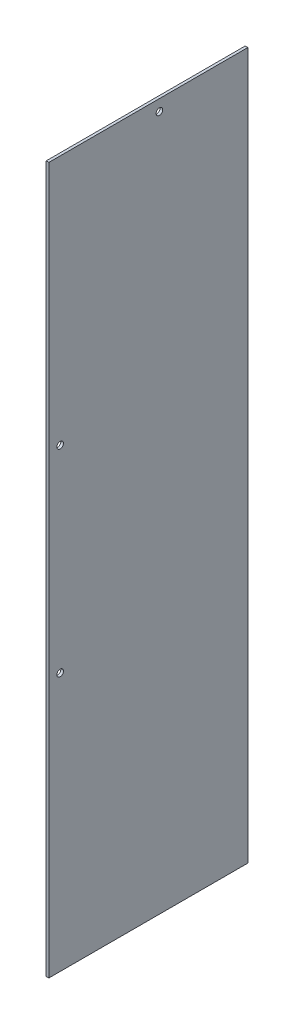
SolidWorks part; units mm, degrees
material "Acrylic (Medium-high impact)"
ref_plane "Front Plane" through (0, 0, 0) normal (0, 0, 1) x (1, 0, 0)
ref_plane "Top Plane" through (0, 0, 0) normal (0, 1, 0) x (1, 0, 0)
ref_plane "Right Plane" through (0, 0, 0) normal (1, 0, 0) x (0, 0, -1)
sketch "Sketch1" plane through (0, 0, 0) normal (1, 0, 0) x (0, 0, -1)
  line L1 (114.4905, -406.5905) -> (-114.4905, -406.5905)
  line L2 (114.4905, -406.5905) -> (114.4905, 406.5905)
  line L3 (114.4905, 406.5905) -> (-114.4905, 406.5905)
  line L4 (-114.4905, -406.5905) -> (-114.4905, 406.5905)
  line L5 (114.4905, -406.5905) -> (-114.4905, 406.5905) construction
  line L6 (114.4905, 406.5905) -> (-114.4905, -406.5905) construction
  point P0 (0, 0)
  dimension "D1" = 813.181
  dimension "D2" = 228.981
extrude "Boss-Extrude1" add sketch "Sketch1" along normal blind 3.0734
sketch "Sketch2" plane through (3.0734, 0, 0) normal (1, 0, 0) x (0, 0, -1)
  line L0 (-114.4905, 406.5905) -> (-114.4905, -406.5905) construction
  line L1 (114.4905, 406.5905) -> (-114.4905, 406.5905) construction
  circle A0 centre (12.7889, 393.6111) radius 3.81
  circle A1 centre (-101.5111, 118.165) radius 3.81
  circle A2 centre (-101.5111, -108.9194) radius 3.81
  dimension "D1" = 7.62
  dimension "D2" = 127.2794
  dimension "D3" = 12.9794
  dimension "D4" = 12.9794
  dimension "D5" = 288.4255
  dimension "D6" = 227.0845
extrude "Cut-Extrude1" cut sketch "Sketch2" against normal up to next
equation "\"Height\"= 32in"
equation "\"Width\"= 23in"
equation "\"Depth\"= 20in"
equation "\"Plexi\"= .121in"
equation "\"EBWidth\" = 9in"
equation "\"MagnetThickness\"= 0.125in"
equation "\"MagnetDiameter\"= 12mm"
equation "\"DoorPlexi\" = \"Plexi\""
equation "\"BasePlateThickness\" = 0.5in"
equation "\"BasePlateWidth\" = \"Width\"+\"EBWidth\"-2*\"Plexi\""
equation "\"BasePlateDepth\" = \"TopBarDepth\"+2*\"CornerCube\""
equation "\"Boxsize\" = .75in"
equation "\"BoxsizeHalf\" = \"Boxsize\"/2"
equation "\"Boxinner\" = .625in"
equation "\"CornerCube\" = 0.75in"
equation "\"FingerLength\" = 1.125in"
equation "\"FingerWidth\" = .625in"
equation "\"Cutwidth\"= .016in"
equation "\"Earsize\"= 1in + \"Cutwidth\" /2"
equation "\"Slotsize\" = 1in - \"CutWidth\" / 2"
equation "\"InnerWidth\" = \"Width\" - 2* \"Plexi\""
equation "\"InnerHeight\" = \"Height\" -2 * \"Plexi\""
equation "\"InnerDepth\" = \"Depth\" - 2*\"Plexi\""
equation "\"RearNumHoles\" = 4"
equation "\"RearHolesBorder\" = 2.25"
equation "\"RearHoleSpacing\" = (\"Width\" - 2*\"RearHolesBorder\") / (\"RearNumHoles\"-1)"
equation "\"RearBarLength\" = (\"InnerWidth\"-2*\"CornerCube\")"
equation "\"RearTopNumHoles\" = 4"
equation "\"RearTopHolesBorder\" = 3.1"
equation "\"RearTopHolesSpacing\" = (\"Width\" - 2*\"RearTopHolesBorder\") / (\"RearTopNumHoles\"-1)"
equation "\"SideTopNumHoles\" = 4"
equation "\"SideTopHoleOffset\"=\"CornerCube\"+\"FingerLength\"+\"Plexi\"+.5"
equation "\"SideHorizNumHoles\" = 4"
equation "\"SideHorizHoleBorder\" = 1.50"
equation "\"SideVertBarLength\"=\"Height\"-\"BasePlateThickness\"-2*\"CornerCube\"-\"Plexi\""
equation "\"SideVertNumHoles\" = 4"
equation "\"SideVertHolesBorder\" = \"CornerCube\"+\"FingerLength\"+1.50"
equation "\"SideVertHoleSpacing\" = (\"SideVertBarLength\" - 2*(\"SideVertHolesBorder\"-\"Plexi\"-\"CornerCube\")) / (\"SideVertNumHoles\"-1)"
equation "\"RearSideVertNumHoles\" = 4"
equation "\"RearSideVertHolesBorder\" = 2.4"
equation "\"RearSideVertHoleSpacing\" = (\"SideVertBarLength\" - 2*(\"RearSideVertHolesBorder\"-\"Plexi\"-\"CornerCube\")) / (\"RearSideVertNumHoles\"-1)"
equation "\"RivetDia\" = .228in"
equation "\"SlotDepth\" = \"Plexi\" + 0.75in + .005in"
equation "\"SideSlotWidth\"   = \"Plexi\"+.005in"
equation "\"SidePanelVertSpacing\" = (\"Height\"-2*(1.75-\"Plexi\")) / 5"
equation "\"BottomPanelSideHoleSpacing\" = (\"InnerDepth\"-2*(1.75-\"Plexi\")) / 4"
equation "\"FrontDoorGap\" = .1in"
equation "\"TopDepth\" = \"Depth\"-\"DoorPlexi\"-\"FrontDoorGap\""
equation "\"TopBarDepth\" = \"Depth\"-\"DoorPlexi\"-\"Plexi\"-2*\"MagnetThickness\"-2*\"CornerCube\""
equation "\"CoolerDepth\" = 12in"
equation "\"ShelfGap\" = 0.5in"
equation "\"ShelfDepth\" = \"TopBarDepth\"+\"CornerCube\"-\"CoolerDepth\""
equation "\"ShelfBarDepth\"=\"ShelfDepth\"-2*\"CornerCube\""
equation "\"ShelfWidth\" = \"EBWidth\"-\"ShelfGap\""
equation "\"ShelfBarWidth\" = \"EBWidth\"-\"Boxsize\""
equation "\"ShelfBarWidthShort\" = \"ShelfBarWidth\"-\"Boxsize\"-\"ShelfGap\""
equation "\"IntakeWidth\"=4in"
equation "\"IntakeHeight\"=2in"
equation "\"ExhaustWidth\"=4in"
equation "\"ExhaustHeight\"=2in"
equation "\"VentSpacing\"=7in"
equation "\"AngleBracketLength\"=20mm"
equation "\"AngleBracketWidth\"=.5in"
equation "\"AngleBracketThickness\"=.125in"
equation "\"AngleBracketHolePos\"=15mm"
equation "\"AngleBracketHoleDia\"=\"Rivet3_16Dia\""
equation "\"ShelfBarAngleHole\"=\"ShelfGap\"+\"Boxsize\"+\"AngleBracketHolePosShort\""
equation "\"D1@Sketch1\"=\"Height\"+\"RivNutHeight\""
equation "\"D2@Sketch1\"=\"EBWidth\"+\"RivNutHeight\""
equation "\"D1@Boss-Extrude1\"=\"DoorPlexi\""
equation "\"ComponentMountDia\"=0.1770"
equation "\"ShelfThickness\" = .1250in"
equation "\"SideTopHoleSpacing\" = (\"TopBarDepth\"-2*\"SideTopHoleOffset\") / (\"SideTopNumHoles\"-1)"
equation "\"SideHorizHoleSpacing\" = (\"TopBarDepth\"-2*\"SideHorizHoleBorder\") / (\"SideHorizNumHoles\"-1)"
equation "\"Rivet3_16Dia\" = .191in"
equation "\"BinderPostDia\" = .228in"
equation "\"ShelfHeight1\" = 13in"
equation "\"ShelfHeight2\" = 24in"
equation "\"VentVertLocation\"=12.75in"
equation "\"AngleBracketLengthShort\"=.625in"
equation "\"AngleBracketLengthLong\"=1in"
equation "\"AngleBracketHolePosShort\"=.358in"
equation "\"AngleBracketHolePosLong\"=.7in"
equation "\"PSBracketThickness\" = .0641in"
equation "\"EBForwardMountOffset\" = 4.0in"
equation "\"EBForwardMount\" = 2*\"Boxsize\"+\"CoolerDepth\"+\"EBForwardMountOffset\""
equation "\"EBRearwardMountOffset\" = 1.5in"
equation "\"EBRearwardMount\"= \"Boxsize\"+\"EBRearwardMountOffset\""
equation "\"MagSealWidth\" = \"InnerWidth\""
equation "\"MagSealHeight\" = \"Height\"-\"BasePlateThickness\"-\"Plexi\""
equation "\"MagWidth\" = .500in"
equation "\"SiliconeSealOD\" = .3125in"
equation "\"SiliconeSealID\" = .1875in"
equation "\"SiliconeSealWidth\" = \"MagSealWidth\" - 2*\"MagWidth\"-\"SiliconeSealOD\""
equation "\"SiliconeSealHeigth\" = \"MagSealHeight\" - 2*\"MagWidth\"-\"SiliconeSealOD\""
equation "\"HooknLoopThick\" = .085in"
equation "\"HooknLoopWidth\" = 0.75in"
equation "\"HooknLoopHeigth\" = 0.75in"
equation "\"RivNutHeight\" = 0.015in"
equation "\"D2@Sketch2\"=\"Plexi\"+\"RivNutHeight\"+\"CornerCube\"+\"ShelfBarWidth\"/2"
equation "\"D3@Sketch2\"=\"Plexi\"+\"RivNutHeight\"+\"BoxsizeHalf\""
equation "\"D4@Sketch2\"=\"Plexi\"+\"RivNutHeight\"+\"BoxsizeHalf\""
equation "\"D5@Sketch2\"=\"RearSideVertHolesBorder\"+\"RearSideVertHoleSpacing\"+\"RivNutHeight\""
equation "\"D6@Sketch2\"=\"RearSideVertHoleSpacing\""
